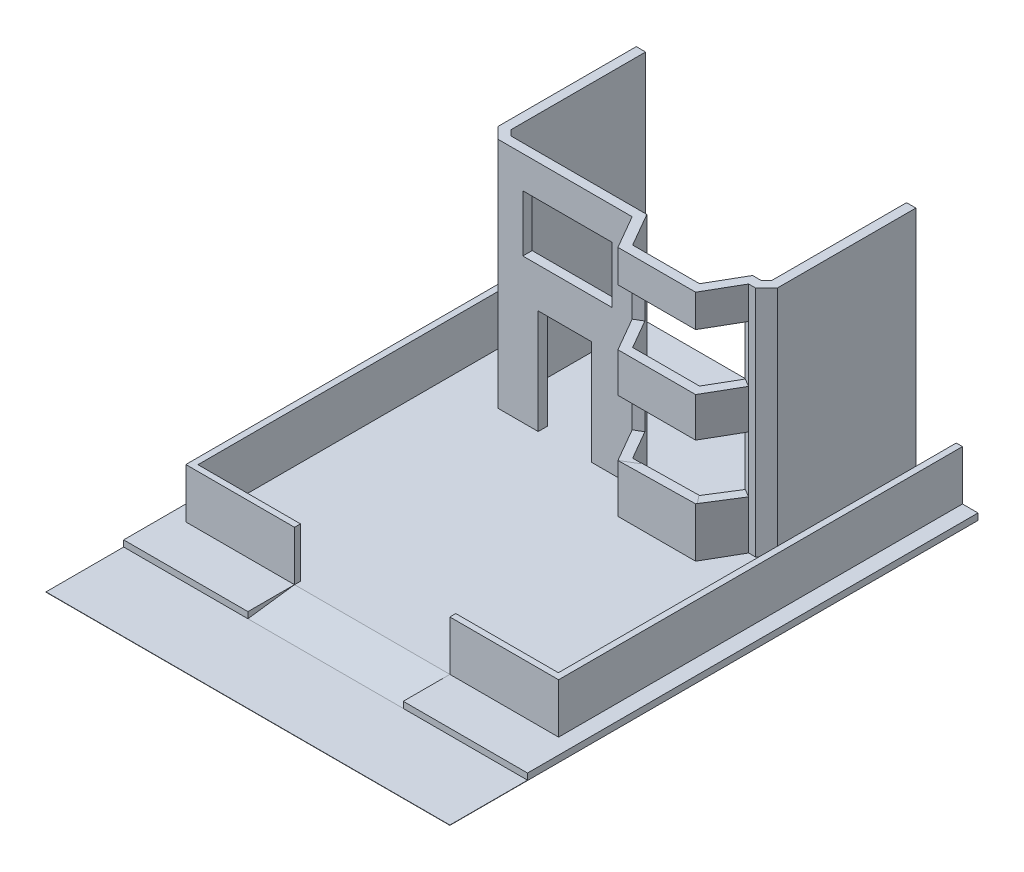
SolidWorks part; units mm, degrees
ref_plane "Alzado" through (0, 0, 0) normal (0, 0, 1) x (1, 0, 0)
ref_plane "Planta" through (0, 0, 0) normal (0, 1, 0) x (1, 0, 0)
ref_plane "Vista lateral" through (0, 0, 0) normal (1, 0, 0) x (0, 0, -1)
sketch "Croquis1" plane through (0, 0, 0) normal (0, 1, 0) x (1, 0, 0)
  line L1 (6500, -8500) -> (-6500, -8500)
  line L2 (6500, -8500) -> (6500, 8500)
  line L3 (6500, 8500) -> (-6500, 8500)
  line L4 (-6500, -8500) -> (-6500, 8500)
  line L5 (6500, -8500) -> (-6500, 8500) construction
  line L6 (6500, 8500) -> (-6500, -8500) construction
  point P0 (0, 0)
  dimension "D1" = 13000
  dimension "D2" = 17000
extrude "Saliente-Extruir1" add sketch "Croquis1" along normal blind 10
sketch "Croquis2" plane through (0, 10, 0) normal (0, 1, 0) x (1, 0, 0)
  line L0 (6500, -8500) -> (6500, 8500) construction
  line L1 (-6500, 8500) -> (6500, 8500)
  line L2 (-6500, 8500) -> (-6500, -6000)
  line L3 (-6500, -6000) -> (6500, -6000)
  line L4 (6500, 8500) -> (6500, -6000)
  line L5 (-6500, -8500) -> (6500, -8500) construction
  dimension "D1" = 2500
extrude "Saliente-Extruir2" add sketch "Croquis2" along normal blind 200
sketch "Croquis4" plane through (0, 210, 0) normal (0, 1, 0) x (1, 0, 0)
  line L0 (-6500, 8500) -> (6500, -6000) construction
  line L1 (-6500, 8500) -> (-6500, -6000) construction
  line L2 (-6000, -4500) -> (6000, -4500)
  line L3 (-6000, -4500) -> (-6000, 7000)
  line L4 (-6000, 7000) -> (6000, 7000)
  line L5 (6000, -4500) -> (6000, 7000)
  line L6 (-6000, -4500) -> (6000, 7000) construction
  line L7 (-6000, 7000) -> (6000, -4500) construction
  line L8 (-6500, -6000) -> (6500, -6000) construction
  line L11 (-5800, -4308.3333) -> (5800, -4308.3333)
  line L12 (-5800, -4308.3333) -> (-5800, 6808.3333)
  line L13 (-5800, 6808.3333) -> (5800, 6808.3333)
  line L14 (5800, -4308.3333) -> (5800, 6808.3333)
  line L15 (-5800, -4308.3333) -> (5800, 6808.3333) construction
  line L16 (-5800, 6808.3333) -> (5800, -4308.3333) construction
  point P4 (0, 1250)
  point P13 (0, 1250)
  dimension "D1" = 500
  dimension "D2" = 1500
  dimension "D3" = 200
extrude "Saliente-Extruir4" add sketch "Croquis4" along normal blind 1600
sketch "Croquis5" plane through (0, 0, 4500) normal (0, 0, 1) x (1, 0, 0)
  line L0 (-6000, 1810) -> (6000, 210) construction
  line L1 (-6000, 1810) -> (6000, 1810) construction
  line L2 (-2500, 210) -> (2500, 210)
  line L3 (-2500, 210) -> (-2500, 1810)
  line L4 (-2500, 1810) -> (2500, 1810)
  line L5 (2500, 210) -> (2500, 1810)
  line L6 (-2500, 210) -> (2500, 1810) construction
  line L7 (-2500, 1810) -> (2500, 210) construction
  point P4 (0, 1010)
  point P11 (-2500, 1010)
  point P12 (2500, 1010)
  dimension "D1" = 5000
extrude "Cortar-Extruir1" cut sketch "Croquis5" against normal up to surface (191.6667 mm away) up to face at (0, 1010, 4308.3333)
sketch "Croquis7" plane through (0, 0, -6808.3333) normal (0, 0, 1) x (1, 0, 0)
  line L0 (5800, 210) -> (-5800, 210) construction
  line L1 (-5800, 1810) -> (5800, 1810)
  line L2 (-5800, 1810) -> (-5800, 210)
  line L3 (-5800, 210) -> (5800, 210)
  line L4 (5800, 1810) -> (5800, 210)
extrude "Cortar-Extruir2" cut sketch "Croquis7" against normal up to surface (191.6667 mm away) up to face at (0, 1010, -7000)
sketch "Croquis8" plane through (0, 210, 0) normal (0, 1, 0) x (1, 0, 0)
  line L0 (-6500, -6000) -> (6500, -6000) construction
  line L1 (-2500, -4500) -> (2500, -4500)
  line L2 (-2500, -4500) -> (-2500, -6000)
  line L3 (-2500, -6000) -> (2500, -6000)
  line L4 (2500, -4500) -> (2500, -6000)
  point P7 (2500, -5250)
  dimension "D1" = 5000
extrude "Cortar-Extruir3" cut sketch "Croquis8" against normal up to surface (200 mm away) up to face at (0, 10, 7250)
sketch "Croquis9" plane through (-2500, 0, 0) normal (1, 0, 0) x (0, 0, -1)
  line L0 (-6000, 10) -> (-4500, 10)
  line L1 (-4500, 10) -> (-4500, 210)
  line L2 (-4500, 210) -> (-6000, 10)
extrude "Saliente-Extruir5" add sketch "Croquis9" along normal up to surface (5000 mm away) up to face at (2500, 110, 5250)
sketch "Croquis10" plane through (0, 210, 0) normal (0, 1, 0) x (1, 0, 0)
  line L0 (6500, 8500) -> (-6500, 8500) construction
  line L1 (-4500, 8500) -> (4500, 8500) construction
  line L2 (-4500, 8500) -> (-4500, 3691.6667) construction
  line L3 (-4500, 3691.6667) -> (4500, 3691.6667) construction
  line L4 (4500, 8500) -> (4500, 3691.6667) construction
  line L5 (-5800, 7000) -> (-5800, -4308.3333) construction
  line L6 (5800, -4308.3333) -> (5800, 7000) construction
  line L7 (2500, -4308.3333) -> (5800, -4308.3333) construction
  line L8 (175.8117, 3691.6667) -> (800.8117, 2609.1349)
  line L9 (800.8117, 2609.1349) -> (3300.8117, 2609.1349)
  line L10 (3300.8117, 2609.1349) -> (3925.8117, 3691.6667)
  line L11 (3925.8117, 3691.6667) -> (4146.4466, 3691.6667)
  line L12 (4146.4466, 3691.6667) -> (4500, 4045.2201)
  line L13 (175.8117, 3691.6667) -> (-4146.4466, 3691.6667)
  line L14 (-4500, 4045.2201) -> (-4146.4466, 3691.6667)
  line L15 (-4500, 4045.2201) -> (-4500, 8500)
  line L16 (-4500, 8500) -> (4500, 8500)
  line L17 (4500, 8500) -> (4500, 4045.2201)
  line L18 (-4200, 8500) -> (-4200, 4169.4841)
  line L19 (-4200, 4169.4841) -> (-4022.1825, 3991.6667)
  line L20 (-4022.1825, 3991.6667) -> (349.0168, 3991.6667)
  line L21 (349.0168, 3991.6667) -> (974.0168, 2909.1349)
  line L22 (974.0168, 2909.1349) -> (3127.6067, 2909.1349)
  line L23 (3127.6067, 2909.1349) -> (3752.6067, 3991.6667)
  line L24 (3752.6067, 3991.6667) -> (4022.1825, 3991.6667)
  line L25 (4022.1825, 3991.6667) -> (4200, 4169.4841)
  line L26 (4200, 4169.4841) -> (4200, 8500)
  line M39 (6500, 8500) -> (-6500, 8500)
  dimension "D1" = 1300
  dimension "D2" = 1300
  dimension "D3" = 8000
  dimension "D4" = 2500
  dimension "D5" = 1250
  dimension "D6" = 1250
  dimension "D7" = 120
  dimension "D8" = 220.6349
  dimension "D9" = 500
  dimension "D10" = 45
  dimension "D11" = 500
  dimension "D12" = 45
  dimension "D13" = 300
  dimension "D14" = 300
  dimension "D15" = 300
  dimension "D16" = 300
  dimension "D17" = 300
  dimension "D18" = 300
  dimension "D19" = 300
  dimension "D20" = 300
  dimension "D21" = 300
extrude "Saliente-Extruir6" add sketch "Croquis10" along normal blind 7500 contours L26 L25 L24 L23 L22 L21 L20 L19 L18 L16 L15 L14 L13 L8 L9 L10 L11 L12 L17 M39
sketch "Croquis11" plane through (0, 0, -7000) normal (0, 0, -1) x (-1, 0, 0)
  line L1 (-6000, 1810) -> (-5800, 1810)
  line L2 (-6000, 1810) -> (-6000, 210)
  line L3 (-6000, 210) -> (-5800, 210)
  line L4 (-5800, 1810) -> (-5800, 210)
  line L5 (5800, 1810) -> (6000, 1810)
  line L6 (5800, 1810) -> (5800, 210)
  line L7 (5800, 210) -> (6000, 210)
  line L8 (6000, 1810) -> (6000, 210)
extrude "Saliente-Extruir7" add sketch "Croquis11" along normal up to surface (1500 mm away) up to face at (0, 2675, -8500)
sketch "Croquis12" plane through (0, 0, -3691.6667) normal (0, 0, 1) x (1, 0, 0)
  line L0 (-1129.95, 210) -> (-2846.9977, 210)
  line L1 (175.8117, 210) -> (-4146.4466, 210) construction
  line L2 (-6000, 210) -> (-2500, 210) construction
  line L3 (-2846.9977, 210) -> (-2846.9977, 3572.8256)
  line L4 (-2846.9977, 3572.8256) -> (-1129.95, 3572.8256)
  line L5 (-1129.95, 3572.8256) -> (-1129.95, 210)
extrude "Cortar-Extruir4" cut sketch "Croquis12" against normal through all
sketch "Croquis13" plane through (0, 0, -2609.1349) normal (0, 0, 1) x (1, 0, 0)
  line L0 (800.8117, 1769.0303) -> (3320.8267, 1810)
  line L1 (800.8117, 7710) -> (800.8117, 210) construction
  line L2 (2500, 1810) -> (6000, 1810) construction
  line L3 (3320.8267, 1810) -> (3300.8117, 3585.1109)
  line L4 (3300.8117, 7710) -> (3300.8117, 210) construction
  line L5 (3300.8117, 3585.1109) -> (800.8117, 3585.1109)
  line L6 (800.8117, 3585.1109) -> (800.8117, 1769.0303)
extrude "Cortar-Extruir5" cut sketch "Croquis13" against normal through all
sketch "Croquis14" plane through (1345.8202, 0, 777.0097) normal (0.866, 0, 0.5) x (0.5, 0, -0.866)
  line L0 (3909.983, 3585.1109) -> (5159.983, 3585.1109)
  line L1 (5159.983, 7710) -> (5159.983, 210) construction
  line L2 (5159.983, 3585.1109) -> (5159.983, 1776.3844)
  line L3 (5159.983, 1776.3844) -> (3950.0129, 1810)
  line L4 (3950.0129, 1810) -> (3909.983, 3585.1109)
extrude "Cortar-Extruir6" cut sketch "Croquis14" against normal mid plane 1380
sketch "Croquis15" plane through (1730.3974, 0, -999.0454) normal (-0.866, 0, 0.5) x (0.5, 0, 0.866)
  line L0 (-1859.1712, 3585.1109) -> (-3109.1712, 3585.1109)
  line L1 (-3109.1712, 7710) -> (-3109.1712, 210) construction
  line L2 (-3109.1712, 3585.1109) -> (-3109.1712, 1769.0303)
  line L3 (-3109.1712, 1769.0303) -> (-1859.1712, 1769.0303)
  line L4 (-1859.1712, 1769.0303) -> (-1859.1712, 3585.1109)
extrude "Cortar-Extruir7" cut sketch "Croquis15" against normal blind 540
sketch "Croquis16" plane through (0, 0, -2609.1349) normal (0, 0, 1) x (1, 0, 0)
  line L0 (800.8117, 6665.6486) -> (3300.8117, 6665.6486)
  line L1 (800.8117, 7710) -> (800.8117, 3585.1109) construction
  line L2 (3300.8117, 7710) -> (3300.8117, 3585.1109) construction
  line L3 (3300.8117, 6665.6486) -> (3300.8117, 4855.6486)
  line L4 (3300.8117, 4855.6486) -> (800.8117, 4855.6486)
  line L5 (800.8117, 4855.6486) -> (800.8117, 6665.6486)
  dimension "D1" = 1810
extrude "Cortar-Extruir8" cut sketch "Croquis16" against normal blind 540
sketch "Croquis17" plane through (1345.8202, 0, 777.0097) normal (0.866, 0, 0.5) x (0.5, 0, -0.866)
  line L0 (3909.983, 6665.6486) -> (5159.983, 6665.6486)
  line L1 (5159.983, 7710) -> (5159.983, 3585.1109) construction
  line L2 (5159.983, 6665.6486) -> (5159.983, 4855.6486)
  line L3 (5159.983, 4855.6486) -> (3909.983, 4855.6486)
  line L4 (3909.983, 4855.6486) -> (3909.983, 6665.6486)
extrude "Cortar-Extruir9" cut sketch "Croquis17" against normal blind 540
sketch "Croquis18" plane through (1730.3974, 0, -999.0454) normal (-0.866, 0, 0.5) x (0.5, 0, 0.866)
  line L0 (-1859.1712, 6665.6486) -> (-3109.1712, 6665.6486)
  line L1 (-3109.1712, 7710) -> (-3109.1712, 3585.1109) construction
  line L2 (-3109.1712, 6665.6486) -> (-3109.1712, 4855.6486)
  line L3 (-3109.1712, 4855.6486) -> (-1859.1712, 4855.6486)
  line L4 (-1859.1712, 4855.6486) -> (-1859.1712, 6665.6486)
extrude "Cortar-Extruir10" cut sketch "Croquis18" against normal blind 540
sketch "Croquis19" plane through (0, 0, -3691.6667) normal (0, 0, 1) x (1, 0, 0)
  line L0 (-478.8763, 6673.6172) -> (-478.8763, 4855.6486)
  line L1 (-478.8763, 4855.6486) -> (-3343.807, 4855.6486)
  line L2 (-3343.807, 4855.6486) -> (-3343.807, 6673.6172)
  line L3 (-3343.807, 6673.6172) -> (-478.8763, 6673.6172)
extrude "Cortar-Extruir11" cut sketch "Croquis19" against normal blind 540
sketch3d "Croquis3D1" [suppressed]
  point P0 (1211.3273, 4855.6486, -2833.7081)
